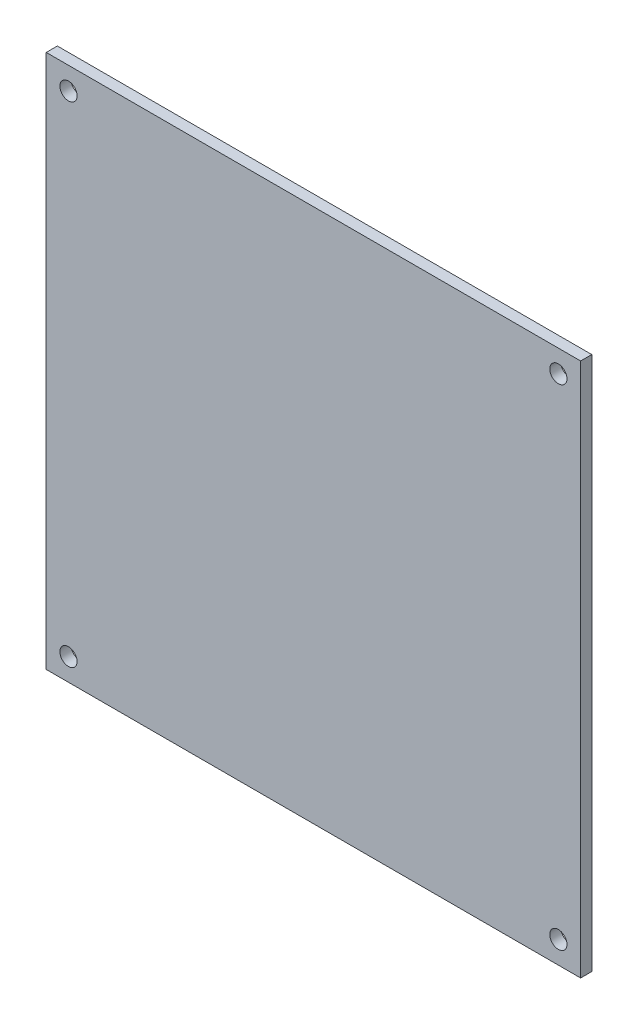
SolidWorks part; units mm, degrees
ref_plane "Front Plane" through (0, 0, 0) normal (0, 0, 1) x (1, 0, 0)
ref_plane "Top Plane" through (0, 0, 0) normal (0, 1, 0) x (1, 0, 0)
ref_plane "Right Plane" through (0, 0, 0) normal (1, 0, 0) x (0, 0, -1)
sketch "Sketch1" plane through (0, 0, 0) normal (0, 0, 1) x (1, 0, 0)
  line L1 (-76.2, -76.2) -> (76.2, -76.2)
  line L2 (-76.2, -76.2) -> (-76.2, 76.2)
  line L3 (-76.2, 76.2) -> (76.2, 76.2)
  line L4 (76.2, -76.2) -> (76.2, 76.2)
  line L5 (-76.2, -76.2) -> (76.2, 76.2) construction
  line L6 (-76.2, 76.2) -> (76.2, -76.2) construction
  point P0 (0, 0)
  dimension "D1" = 152.4
  dimension "D2" = 152.4
extrude "Boss-Extrude1" add sketch "Sketch1" along normal blind 3.175
sketch "Sketch13" plane through (0, 0, 3.175) normal (0, 0, 1) x (1, 0, 0)
  line L1 (69.85, 69.85) -> (-69.85, 69.85)
  line L2 (69.85, 69.85) -> (69.85, -69.85)
  line L3 (69.85, -69.85) -> (-69.85, -69.85)
  line L4 (-69.85, 69.85) -> (-69.85, -69.85)
  line L5 (69.85, 69.85) -> (-69.85, -69.85) construction
  line L6 (69.85, -69.85) -> (-69.85, 69.85) construction
  point P0 (0, 0)
  dimension "D1" = 139.7
  dimension "D2" = 139.7
hole_wizard "#10 (0.1935) Diameter Hole1" positions "Sketch14" profile "Sketch15" hole size "#10" standard "ANSI Inch" end condition through all
sketch "Sketch14" plane through (0, 0, 3.175) normal (0, 0, 1) x (1, 0, 0)
  point P0 (69.85, -69.85)
  point P3 (-69.85, -69.85)
  point P6 (-69.85, 69.85)
  point P9 (69.85, 69.85)
sketch "Sketch15" plane through (69.85, -69.85, 3.175) normal (1, 0, 0) x (0, -1, 0)
  line L0 (0, 0) -> (0, 3.175)
  line L1 (0, 3.175) -> (2.4574, 3.175)
  line L2 (2.4574, 3.175) -> (2.4574, 0)
  line L5 (2.4574, 0) -> (0, 0)
  line L11 (0, -6.35) -> (0, 107.95) construction
  dimension "Thru Hole Dia." = 4.9149
  dimension "Thru Hole Depth" = 3.175
